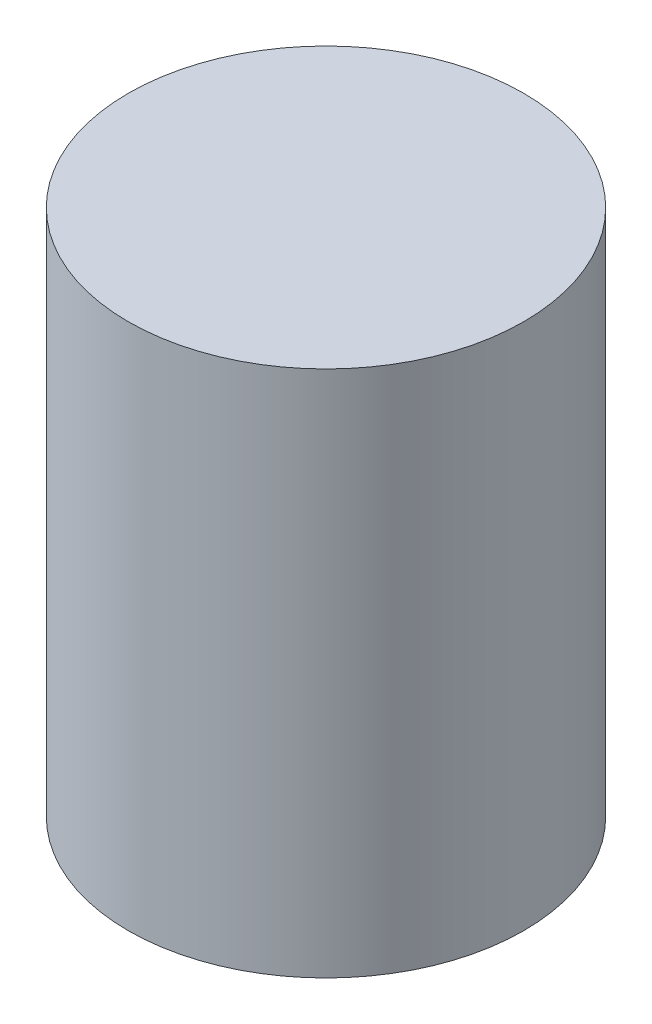
SolidWorks part; units mm, degrees
ref_plane "Alzado" through (0, 0, 0) normal (0, 0, 1) x (1, 0, 0)
ref_plane "Planta" through (0, 0, 0) normal (0, 1, 0) x (1, 0, 0)
ref_plane "Vista lateral" through (0, 0, 0) normal (1, 0, 0) x (0, 0, -1)
sketch "Croquis1" plane through (0, 0, 0) normal (0, 1, 0) x (1, 0, 0)
  circle A0 centre (0, 0) radius 15
  dimension "D1" = 30
extrude "Saliente-Extruir1" add sketch "Croquis1" along normal blind 40
